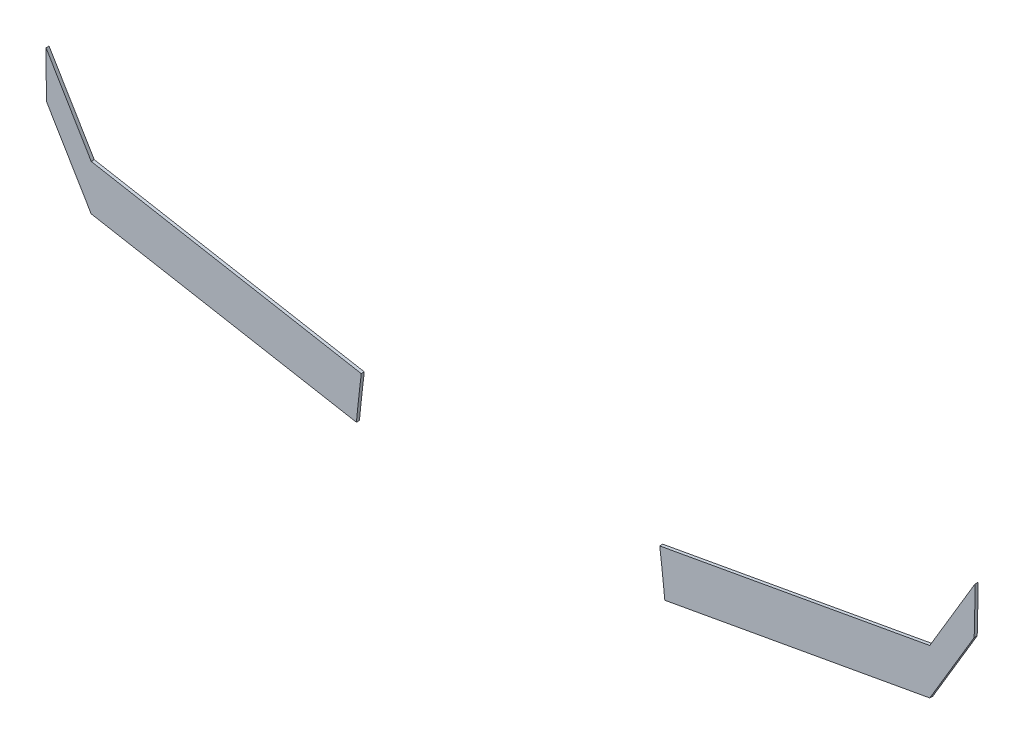
SolidWorks part; units mm, degrees
ref_plane "Alzado" through (0, 0, 0) normal (0, 0, 1) x (1, 0, 0)
ref_plane "Planta" through (0, 0, 0) normal (0, 1, 0) x (1, 0, 0)
ref_plane "Vista lateral" through (0, 0, 0) normal (1, 0, 0) x (0, 0, -1)
sketch "Model" plane through (0, 0, 0) normal (0, 0, 1) x (1, 0, 0)
  line L0 (50.8066, -21.8958) -> (49.3374, -24.3608)
  line L1 (49.3374, -24.3608) -> (40.5942, -25.9401)
  line L2 (20.1977, -21.8987) -> (21.6663, -24.3622)
  line L3 (21.6663, -24.3622) -> (30.4186, -25.9415)
  line L4 (50.8284, -20.3593) -> (49.3374, -22.8608)
  line L5 (49.3374, -22.8608) -> (40.4267, -24.4704)
  line L6 (20.1761, -20.3616) -> (21.6674, -22.8629)
  line L7 (21.6674, -22.8629) -> (30.5783, -24.4711)
  arc A0 (50.8017, -21.9042) -> (50.8284, -20.3593) centre (0.7611, -20.266) ccw
  arc A1 (40.5942, -25.9401) -> (40.4267, -24.4704) centre (-17.4191, -31.8093) ccw
  arc A2 (20.1761, -20.3616) -> (20.1977, -21.8987) centre (74.3249, -20.3684) ccw
  arc A3 (30.5783, -24.4711) -> (30.4186, -25.9415) centre (83.6478, -30.9789) ccw
extrude "Saliente-Extruir1" add sketch "Model" along normal blind 0.1 contours A3 L7 L6 A2 L2 L3 | A1 L1 L0 A0 L4 L5
